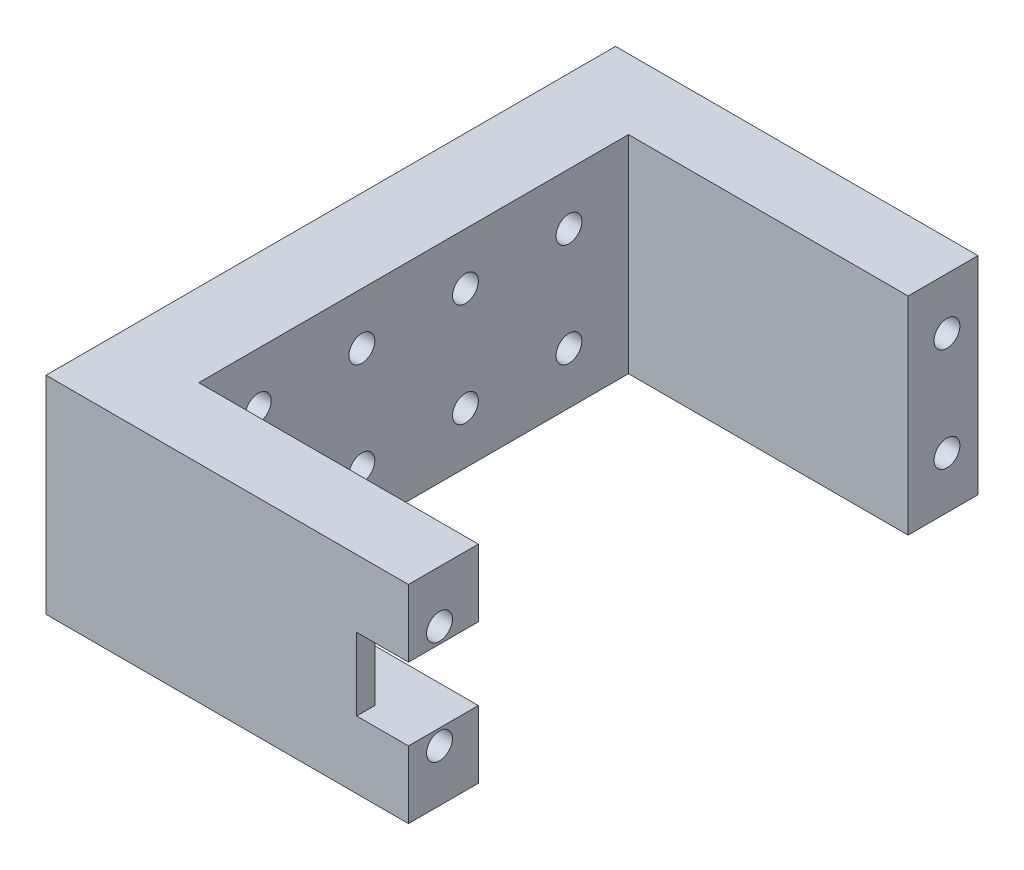
SolidWorks part; units mm, degrees
ref_plane "Front Plane" through (0, 0, 0) normal (0, 0, 1) x (1, 0, 0)
ref_plane "Top Plane" through (0, 0, 0) normal (0, 1, 0) x (1, 0, 0)
ref_plane "Right Plane" through (0, 0, 0) normal (1, 0, 0) x (0, 0, -1)
sketch "Sketch1" plane through (0, 0, 0) normal (1, 0, 0) x (0, 0, -1)
  line L1 (-27.5, -10) -> (27.5, -10)
  line L2 (-27.5, -10) -> (-27.5, 10)
  line L3 (-27.5, 10) -> (27.5, 10)
  line L4 (27.5, -10) -> (27.5, 10)
  line L5 (-27.5, -10) -> (27.5, 10) construction
  line L6 (-27.5, 10) -> (27.5, -10) construction
  point P0 (0, 0)
  dimension "D1" = 20
  dimension "D2" = 55
extrude "Main" add sketch "Sketch1" along normal mid plane 35
sketch "Sketch3" plane through (0, 10, 0) normal (0, 1, 0) x (1, 0, 0)
  line L0 (17.5, 27.5) -> (17.5, -27.5) construction
  line L1 (17.5, 20.75) -> (-9.5, 20.75)
  line L2 (17.5, 20.75) -> (17.5, -20.75)
  line L3 (17.5, -20.75) -> (-9.5, -20.75)
  line L4 (-9.5, 20.75) -> (-9.5, -20.75)
  line L6 (17.5, 27.5) -> (-17.5, 27.5) construction
  line L7 (17.5, -27.5) -> (-17.5, -27.5) construction
  line L8 (-17.5, 27.5) -> (-17.5, -27.5) construction
  dimension "D1" = 8
  dimension "D3" = 41.5
  dimension "D4" = 6.75
  dimension "D5" = 6.75
extrude "CentralHoleForServo" cut sketch "Sketch3" against normal through all
sketch "Sketch4" plane through (17.5, 0, 0) normal (1, 0, 0) x (0, 0, -1)
  circle A0 centre (-24.5, 5) radius 1.25
  circle A1 centre (-24.5, -5) radius 1.25
  dimension "D1" = 2.5
  dimension "D2" = 5
  dimension "D3" = 5
  dimension "D4" = 24.5
extrude "FixHoleServo" cut sketch "Sketch4" against normal blind 12
mirror "FixHoleServoMirror" about plane through (0, 0, 0) normal (0, 0, 1) of "FixHoleServo"
sketch "Sketch5" plane through (-17.5, 0, 0) normal (-1, 0, 0) x (0, 0, 1)
  line L0 (15, 5) -> (15, -5) construction
  circle A0 centre (15, 5) radius 1.25
  circle A1 centre (15, -5) radius 1.25
  point P4 (15, 0)
  dimension "D1" = 2.5
  dimension "D2" = 10
  dimension "D3" = 15
extrude "BottomFixHole" cut sketch "Sketch5" against normal blind 12
pattern_linear "LPattern1" count 4 spacing 10 along (0, 0, -1) of "BottomFixHole"
sketch "Sketch6" plane through (17.5, 0, 0) normal (1, 0, 0) x (0, 0, -1)
  line L0 (-20.75, -10) -> (-20.75, 10) construction
  line L1 (-25.75, 3.5) -> (-20.75, 3.5)
  line L2 (-25.75, 3.5) -> (-25.75, -3.5)
  line L3 (-25.75, -3.5) -> (-20.75, -3.5)
  line L4 (-20.75, 3.5) -> (-20.75, -3.5)
  point P6 (-25.75, 0)
  dimension "D1" = 7
  dimension "D2" = 5
extrude "Cut-Extrude4" cut sketch "Sketch6" against normal up to surface (27 mm away) up to face at (-9.5, 5, 6.25)
sketch "Sketch7" plane through (17.5, 0, 0) normal (1, 0, 0) x (0, 0, -1)
  line L0 (-27.5, 10) -> (-27.5, -10) construction
  line L1 (-25.75, -3.5) -> (-27.5, -3.5)
  line L2 (-25.75, -3.5) -> (-25.75, 3.5)
  line L3 (-25.75, 3.5) -> (-27.5, 3.5)
  line L4 (-27.5, -3.5) -> (-27.5, 3.5)
  point P5 (-25.75, 3.5)
  point P7 (-27.5, 3.5)
extrude "Cut-Extrude5" cut sketch "Sketch7" against normal blind 5
